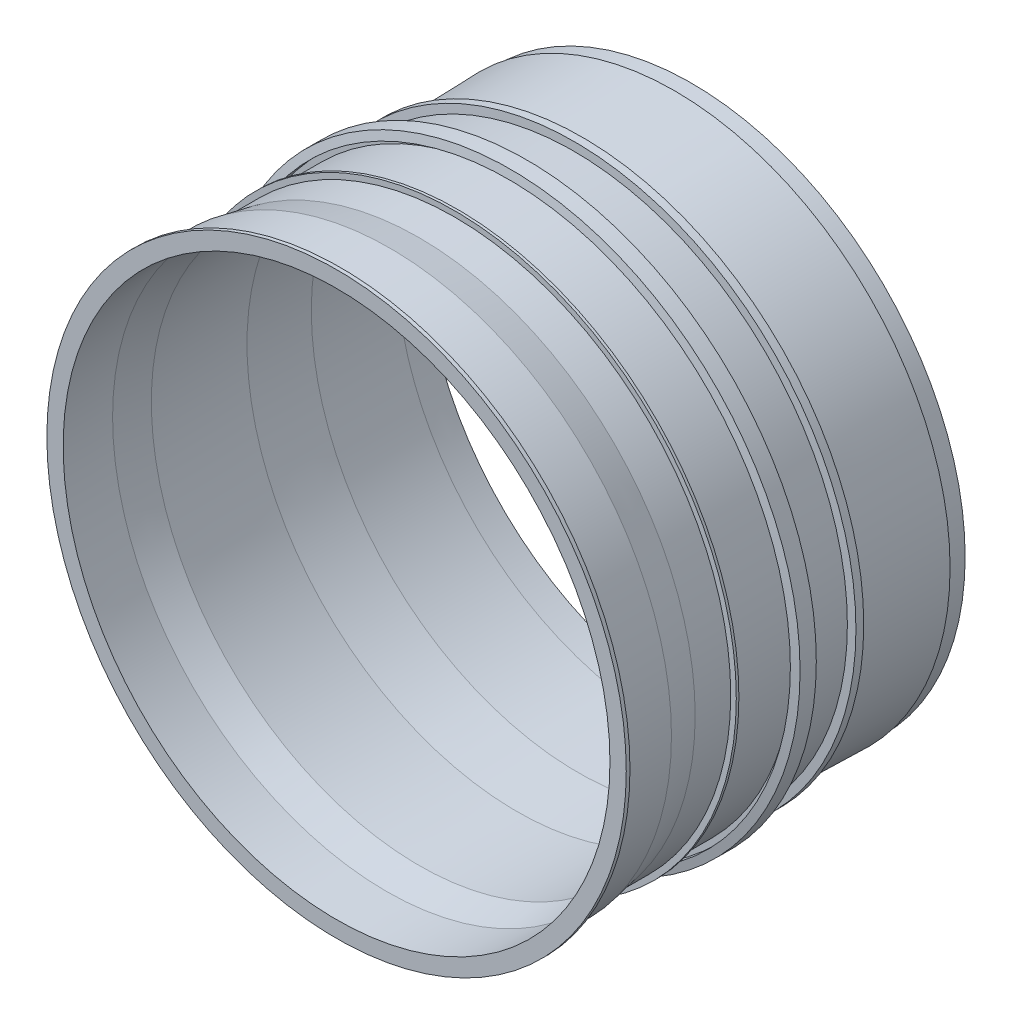
SolidWorks part; units mm, degrees
ref_plane "Front Plane" through (0, 0, 0) normal (0, 0, 1) x (1, 0, 0)
ref_plane "Top Plane" through (0, 0, 0) normal (0, 1, 0) x (1, 0, 0)
ref_plane "Right Plane" through (0, 0, 0) normal (1, 0, 0) x (0, 0, -1)
sketch "Sketch1" plane through (0, 0, 0) normal (1, 0, 0) x (0, 0, -1)
  line L0 (31.8024, 848.4909) -> (1294.8478, 848.4909) construction
sketch "Sketch3" plane through (0, 0, 0) normal (1, 0, 0) x (0, 0, -1)
  line L0 (625.2431, 1107.2778) -> (625.2431, 1173.2927)
  line L1 (625.2431, 1173.2927) -> (640.2465, 1173.2927)
  line L2 (640.2465, 1173.2927) -> (640.2465, 1140.2853)
  line L3 (640.2465, 1140.2853) -> (841.2919, 1140.2853)
  line L4 (841.2919, 1140.2853) -> (959.8186, 1117.7802)
  line L5 (959.8186, 1117.7802) -> (1103.8511, 1117.7802)
  line L6 (1103.8511, 1117.7802) -> (1103.8511, 1140.2853)
  line L7 (1103.8511, 1140.2853) -> (1114.3535, 1140.2853)
  line L8 (1114.3535, 1140.2853) -> (1114.3535, 1117.7802)
  line L9 (1114.3535, 1117.7802) -> (1355.908, 1117.7802)
  line L10 (1355.908, 1117.7802) -> (1355.908, 1140.2853)
  line L11 (1355.908, 1140.2853) -> (1322.9006, 1140.2853)
  line L12 (1322.9006, 1140.2853) -> (1329.1678, 1173.2927)
  line L13 (1329.1678, 1173.2927) -> (1394.9168, 1173.2927)
  line L14 (1394.9168, 1173.2927) -> (1412.9538, 1140.2853)
  line L15 (1412.9538, 1140.2853) -> (1373.7337, 1140.2853)
  line L16 (1373.7337, 1140.2853) -> (1373.7337, 1117.7802)
  line L17 (1373.7337, 1117.7802) -> (1586.7931, 1107.2778)
  line L18 (1586.7931, 1107.2778) -> (1588.4201, 1140.2853)
  line L19 (1588.4201, 1140.2853) -> (1619.9676, 1140.2853)
  line L20 (1619.9676, 1140.2853) -> (1619.9676, 1123.7815)
  line L21 (1619.9676, 1123.7815) -> (1619.9676, 1107.2778)
  line L22 (1619.9676, 1107.2778) -> (1994.4714, 1115.5297)
  line L23 (1994.4714, 1115.5297) -> (1994.4714, 1107.2778)
  line L24 (1994.4714, 1107.2778) -> (2063.6982, 1107.2778)
  line L25 (2063.6982, 1107.2778) -> (2063.6982, 1083.7696)
  line L26 (2063.6982, 1083.7696) -> (1949.052, 1081.2435)
  line L27 (1949.052, 1081.2435) -> (1903.2694, 1081.2435)
  line L28 (1903.2694, 1081.2435) -> (1604.1939, 1081.2435)
  line L29 (1604.1939, 1081.2435) -> (1355.908, 1093.4823)
  line L30 (1355.908, 1093.4823) -> (959.8186, 1084.7548)
  line L31 (959.8186, 1084.7548) -> (827.9624, 1109.7908)
  line L32 (827.9624, 1109.7908) -> (625.2431, 1107.2778)
  line L33 (0, 0) -> (4205.9474, 0) construction
revolve "Revolve1" add sketch "Sketch3" angle 360 about L33
